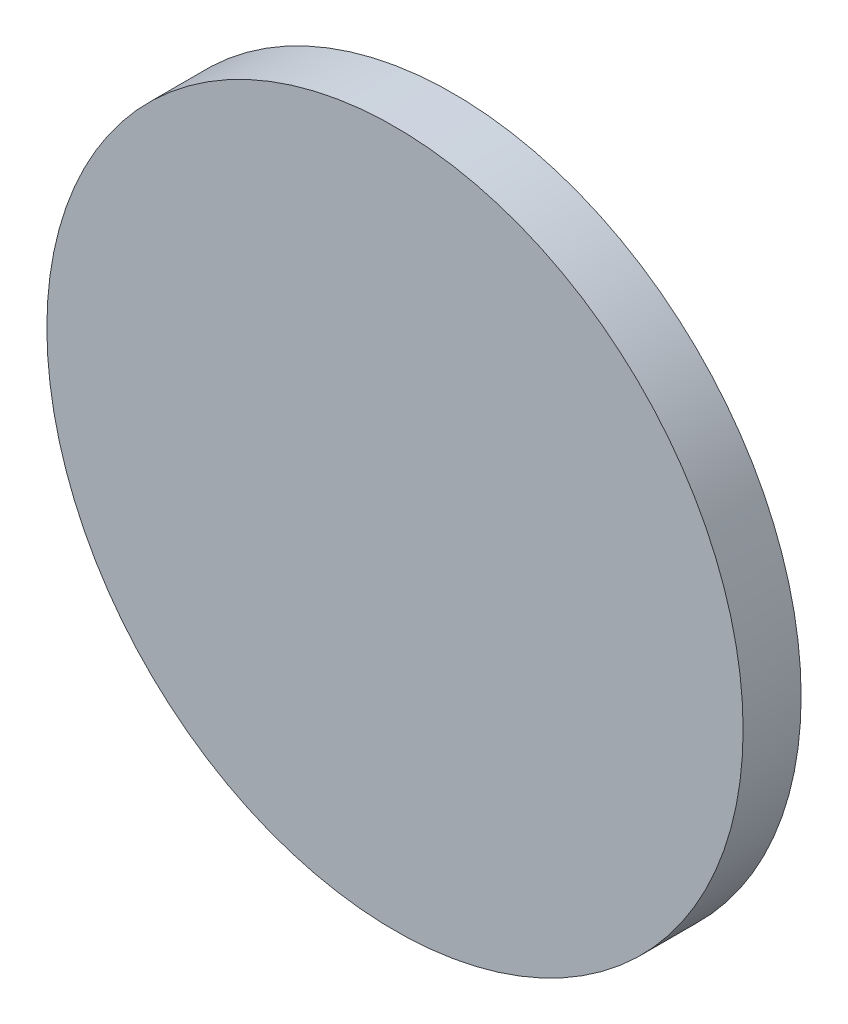
SolidWorks part; units mm, degrees
ref_plane "Front Plane" through (0, 0, 0) normal (0, 0, 1) x (1, 0, 0)
ref_plane "Top Plane" through (0, 0, 0) normal (0, 1, 0) x (1, 0, 0)
ref_plane "Right Plane" through (0, 0, 0) normal (1, 0, 0) x (0, 0, -1)
sketch "Sketch1" plane through (0, 0, 0) normal (0, 0, 1) x (1, 0, 0)
  circle A0 centre (0, 0) radius 38.1
  dimension "D1" = 76.2
extrude "Boss-Extrude1" add sketch "Sketch1" along normal blind 6.35
